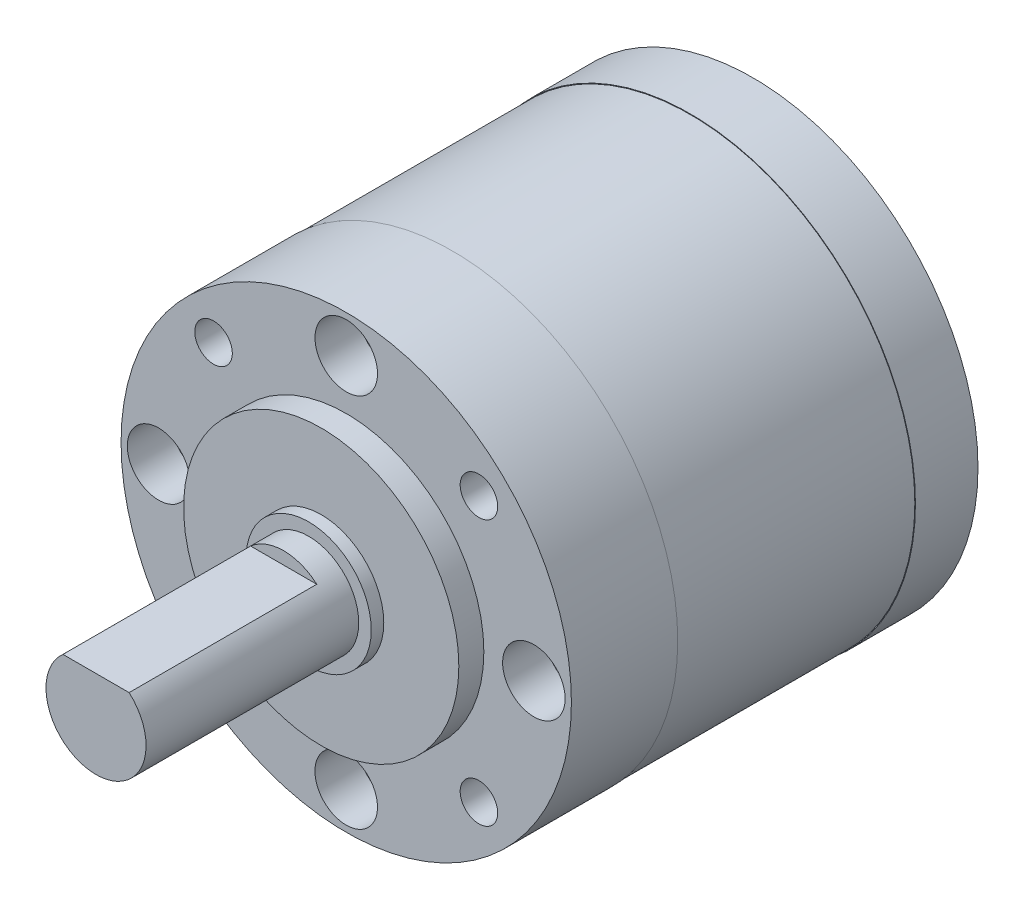
SolidWorks part; units mm, degrees
material "黃銅"
ref_plane "前基準面" through (0, 0, 0) normal (0, 0, 1) x (1, 0, 0)
ref_plane "上基準面" through (0, 0, 0) normal (0, 1, 0) x (1, 0, 0)
ref_plane "右基準面" through (0, 0, 0) normal (1, 0, 0) x (0, 0, -1)
sketch "草圖1" plane through (0, 0, 0) normal (0, 0, 1) x (1, 0, 0)
  circle A0 centre (0, 0) radius 18
  dimension "D1" = 36
extrude "填料-伸長1" add sketch "草圖1" along normal blind 8.5
sketch "草圖2" plane through (0, 0, 0) normal (0, 0, -1) x (-1, 0, 0)
  circle A0 centre (0, 0) radius 17.95
  dimension "D1" = 35.9
extrude "填料-伸長2" add sketch "草圖2" along normal blind 19
sketch "草圖3" plane through (0, 0, -19) normal (0, 0, -1) x (-1, 0, 0)
  circle A0 centre (0, 0) radius 18
extrude "填料-伸長3" add sketch "草圖3" along normal blind 5
sketch "草圖4" plane through (0, 0, 8.5) normal (0, 0, 1) x (1, 0, 0)
  circle A0 centre (0, 0) radius 11
  dimension "D1" = 22
extrude "填料-伸長4" add sketch "草圖4" along normal blind 2
sketch "草圖5" plane through (0, 0, 10.5) normal (0, 0, 1) x (1, 0, 0)
  circle A0 centre (0, 0) radius 5
  dimension "D1" = 10
extrude "填料-伸長5" add sketch "草圖5" along normal blind 1
sketch "草圖6" plane through (0, 0, 11.5) normal (0, 0, 1) x (1, 0, 0)
  circle A0 centre (0, 0) radius 4
  dimension "D1" = 8
extrude "填料-伸長6" add sketch "草圖6" along normal blind 17
sketch "草圖7" plane through (0, 0, 28.5) normal (0, 0, 1) x (1, 0, 0)
  line L0 (-2.6458, 3) -> (2.6458, 3)
  circle A0 centre (0, 0) radius 4 construction
  circle A1 centre (0, 0) radius 4 construction
  circle M2 centre (0, 0) radius 4
  dimension "D1" = 3
extrude "除料-伸長1" cut sketch "草圖7" against normal blind 15 and the other way through all contours L0 M2
sketch "草圖8" plane through (0, 0, -24) normal (0, 0, -1) x (-1, 0, 0)
  circle A0 centre (0, 0) radius 11
  dimension "D1" = 22
extrude "除料-伸長2" cut sketch "草圖8" against normal blind 4
sketch "草圖9" plane through (0, 0, -24) normal (0, 0, -1) x (-1, 0, 0)
  circle A0 centre (0, 0) radius 4
  dimension "D1" = 8
extrude "除料-伸長3" cut sketch "草圖9" against normal blind 17
sketch "草圖10" plane through (0, 0, 8.5) normal (0, 0, 1) x (1, 0, 0)
  line L0 (0, 0) -> (0, 15) construction
  circle A0 centre (0, 15) radius 1.5
  dimension "D2" = 3
  dimension "D1" = 15
extrude "除料-伸長4" cut sketch "草圖10" against normal blind 10
pattern_circular "環狀複製排列1" count 8 over 360 about axis through (0, 0, 0) along (0, 0, 1) of "除料-伸長4"
sketch "草圖11" plane through (0, 0, 8.5) normal (0, 0, 1) x (1, 0, 0)
  circle A0 centre (0, 15) radius 2.5
  dimension "D1" = 5
extrude "除料-伸長5" cut sketch "草圖11" against normal blind 3.5
pattern_circular "環狀複製排列2" count 4 every 90 about axis through (0, 0, 0) along (0, 0, 1) of "除料-伸長5"
